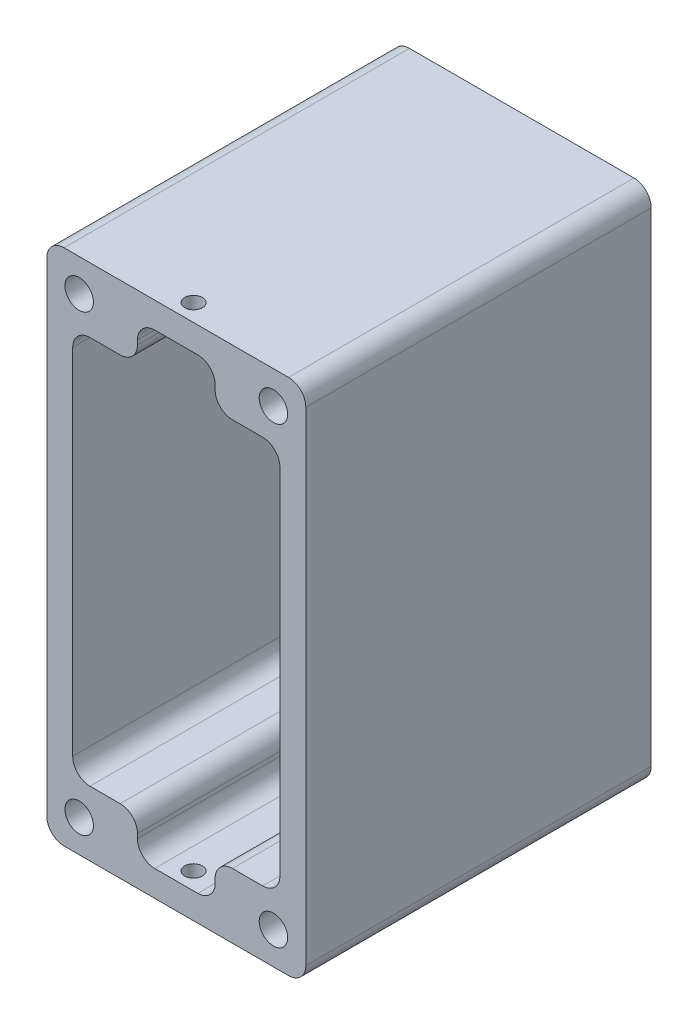
SolidWorks part; units mm, degrees
ref_plane "前视基准面" through (0, 0, 0) normal (0, 0, 1) x (1, 0, 0)
ref_plane "上视基准面" through (0, 0, 0) normal (0, 1, 0) x (1, 0, 0)
ref_plane "右视基准面" through (0, 0, 0) normal (1, 0, 0) x (0, 0, -1)
sketch "草图1" plane through (0, 0, 0) normal (0, 0, 1) x (1, 0, 0)
  line L0 (0, 30) -> (0, -19.5) construction
  line L1 (-12, 0) -> (12, 0) construction
  line L2 (12, 19.5) -> (12, 22.5)
  line L3 (7.5, 30) -> (-7.5, 30)
  line L4 (-12, -19.5) -> (-12, 19.5)
  line L5 (-15, 30) -> (-15, 22.5)
  line L6 (-7.5, 30) -> (-15, 30)
  line L7 (-7.5, 22.5) -> (-4.5, 22.5)
  line L8 (-4.5, 22.5) -> (-4.5, 27)
  line L9 (-15, 22.5) -> (-7.5, 22.5)
  line L10 (-7.5, 30) -> (-7.5, 22.5)
  line L11 (4.5, 27) -> (-4.5, 27)
  line L12 (15, 30) -> (7.5, 30)
  line L13 (15, 22.5) -> (7.5, 22.5)
  line L14 (7.5, 30) -> (7.5, 22.5)
  line L15 (15, 22.5) -> (15, 30)
  line L16 (12, -19.5) -> (12, 19.5)
  line L17 (-7.5, 30) -> (-7.5, 22.5)
  line L18 (-15, 22.5) -> (-7.5, 22.5)
  line L20 (7.5, 30) -> (7.5, 22.5)
  line L21 (15, 22.5) -> (7.5, 22.5)
  line L22 (4.5, 22.5) -> (4.5, 27)
  line L23 (7.5, 22.5) -> (4.5, 22.5)
  line L24 (0, -30) -> (0, 19.5) construction
  line L26 (-15, 22.5) -> (-15, 30)
  line L28 (-12, -19.5) -> (-12, -22.5)
  line L29 (-15, 30) -> (-7.5, 30)
  line L30 (7.5, 30) -> (15, 30)
  line L31 (15, 30) -> (15, 22.5)
  line L32 (-12, 19.5) -> (-12, 22.5)
  line L33 (15, -30) -> (15, -22.5)
  line L34 (7.5, -30) -> (15, -30)
  line L35 (-15, -30) -> (-7.5, -30)
  line L36 (-15, -22.5) -> (-15, -30)
  line L37 (7.5, -22.5) -> (4.5, -22.5)
  line L38 (4.5, -22.5) -> (4.5, -27)
  line L39 (15, -22.5) -> (7.5, -22.5)
  line L40 (7.5, -30) -> (7.5, -22.5)
  line L41 (-15, -22.5) -> (-7.5, -22.5)
  line L42 (-7.5, -30) -> (-7.5, -22.5)
  line L43 (15, -22.5) -> (15, -30)
  line L44 (7.5, -30) -> (7.5, -22.5)
  line L45 (15, -22.5) -> (7.5, -22.5)
  line L46 (15, -30) -> (7.5, -30)
  line L47 (4.5, -27) -> (-4.5, -27)
  line L48 (-7.5, -30) -> (-7.5, -22.5)
  line L49 (-15, -22.5) -> (-7.5, -22.5)
  line L50 (-4.5, -22.5) -> (-4.5, -27)
  line L51 (-7.5, -22.5) -> (-4.5, -22.5)
  line L52 (-7.5, -30) -> (-15, -30)
  line L53 (-15, -30) -> (-15, -22.5)
  line L54 (7.5, -30) -> (-7.5, -30)
  line L55 (12, -19.5) -> (12, -22.5)
  line L56 (-15, 22.5) -> (-15, -22.5)
  line L57 (15, 22.5) -> (15, -22.5)
  line L58 (-7.5, 22.5) -> (-4.5, 22.5)
  line L59 (-4.5, 22.5) -> (-4.5, 27)
  line L60 (4.5, 22.5) -> (4.5, 27)
  line L61 (7.5, 22.5) -> (4.5, 22.5)
  line L62 (-7.5, -22.5) -> (-4.5, -22.5)
  line L63 (-4.5, -22.5) -> (-4.5, -27)
  line L64 (4.5, -27) -> (-4.5, -27)
  line L65 (7.5, -22.5) -> (4.5, -22.5)
  line L66 (4.5, -22.5) -> (4.5, -27)
  circle A0 centre (0, 0) radius 6
  point P0 (0, 0)
extrude "凸台-拉伸1" add sketch "草图1" along normal blind 40 contours L23 L14 L3 L10 L7 L8 L11 L22 | L10 L6 L5 L9 L18 | L13 L15 L12 L14 | L57 L13 L2 L16 L55 L39 | L9 L56 L41 L28 L4 L32 | L35 L42 L41 L36 | L40 L34 L33 L39 L45 | L54 L40 L37 L38 L47 L50 L51 L42
sketch "草图2" plane through (0, 0, 0) normal (0, 0, -1) x (-1, 0, 0)
  line L4 (-15, -30) -> (15, -30)
  line L5 (15, -30) -> (15, 30)
  line L6 (15, 30) -> (-15, 30)
  line L7 (-15, 30) -> (-15, -30)
  line L8 (-15, -30) -> (15, -30)
  line L9 (15, -30) -> (15, 30)
  line L10 (15, 30) -> (-15, 30)
  line L11 (-15, 30) -> (-15, -30)
  line L36 (-12, -22.5) -> (-4.5, -22.5)
  line L37 (-12, 22.5) -> (-12, -22.5)
  line L38 (-4.5, 22.5) -> (-12, 22.5)
  line L39 (-4.5, 27) -> (-4.5, 22.5)
  line L40 (4.5, 27) -> (-4.5, 27)
  line L41 (4.5, 22.5) -> (4.5, 27)
  line L42 (12, 22.5) -> (4.5, 22.5)
  line L43 (12, -22.5) -> (12, 22.5)
  line L44 (4.5, -22.5) -> (12, -22.5)
  line L45 (4.5, -27) -> (4.5, -22.5)
  line L46 (-4.5, -27) -> (4.5, -27)
  line L47 (-4.5, -22.5) -> (-4.5, -27)
  line L48 (-12, -22.5) -> (-4.5, -22.5)
  line L49 (-12, 22.5) -> (-12, -22.5)
  line L50 (-4.5, 22.5) -> (-12, 22.5)
  line L51 (-4.5, 27) -> (-4.5, 22.5)
  line L52 (4.5, 27) -> (-4.5, 27)
  line L53 (4.5, 22.5) -> (4.5, 27)
  line L54 (12, 22.5) -> (4.5, 22.5)
  line L55 (12, -22.5) -> (12, 22.5)
  line L56 (4.5, -22.5) -> (12, -22.5)
  line L57 (4.5, -27) -> (4.5, -22.5)
  line L58 (-4.5, -27) -> (4.5, -27)
  line L59 (-4.5, -22.5) -> (-4.5, -27)
  dimension "D1" = 0
  dimension "D2" = 0
fillet "圆角1" radius 2 12 edges at (12, 22.5, 20) (12, -22.5, 20) (4.5, -22.5, 20) (4.5, -27, 20) (-4.5, -27, 20) (-4.5, -22.5, 20) (-12, -22.5, 20) (-12, 22.5, 20) (-4.5, 22.5, 20) (-4.5, 27, 20) (4.5, 27, 20) (4.5, 22.5, 20)
ref_plane "基准面1" through (0, 30, 0) normal (0, 1, 0) x (1, 0, 0)
sketch "草图3" plane through (0, 30, 0) normal (0, 1, 0) x (1, 0, 0)
  line L0 (0, -28) -> (1.1542, -28) construction
  line L4 (0, -30) -> (0, -26) construction
hole_wizard "M2.5 螺纹孔1" positions "草图10" profile "草图11" tap size "M2.5" standard "GB" end condition through all
sketch "草图10" plane through (0, 30, 0) normal (0, 1, 0) x (1, 0, 0)
  point P0 (0, -38)
sketch "草图11" plane through (0, 30, 38) normal (1, 0, 0) x (0, 0, 1)
  line L0 (0, 0) -> (0, 60)
  line L1 (0, 60) -> (1.025, 60)
  line L2 (1.025, 60) -> (1.025, 0)
  line L5 (1.025, 0) -> (0, 0)
  line L11 (0, -6.35) -> (0, 107.95) construction
  dimension "通孔螺纹孔钻头直径" = 2.05
  dimension "通孔螺纹孔钻头深度" = 60
cosmetic thread "孔螺蚊线1" parameters "D2"=2.5
sketch "草图12" plane through (0, 0, 0) normal (0, 0, 1) x (1, 0, 0)
  circle A17 centre (-11.25, -26.25) radius 1.65
  circle A19 centre (11.25, -26.25) radius 1.65
  circle A21 centre (11.25, 26.25) radius 1.65
  circle A23 centre (-11.25, 26.25) radius 1.65
hole_wizard "M4 螺纹孔1" positions "草图13" profile "草图14" tap size "M4" standard "GB"
sketch "草图13" plane through (0, 0, 0) normal (0, 0, -1) x (-1, 0, 0)
  point P0 (-11.25, 26.25)
  point P3 (11.25, 26.25)
  point P6 (11.25, -26.25)
  point P9 (-11.25, -26.25)
sketch "草图14" plane through (11.25, 26.25, 0) normal (1, 0, 0) x (0, 1, 0)
  line L0 (0, 0) -> (0, 8.9914)
  line L1 (0, 8.9914) -> (1.65, 8)
  line L2 (1.65, 8) -> (1.65, 0)
  line L5 (1.65, 0) -> (0, 0)
  line L10 (0, 8.9914) -> (-1.65, 8) construction
  line L11 (0, -6.35) -> (0, 107.95) construction
  dimension "螺纹孔钻头直径" = 3.3
  dimension "螺纹孔钻头深度" = 8
  dimension "导头角度" = 118
cosmetic thread "孔螺蚊线2" parameters "D1"=8, "D2"=4
cosmetic thread "孔螺蚊线3" parameters "D1"=8, "D2"=4
cosmetic thread "孔螺蚊线4" parameters "D1"=8, "D2"=4
cosmetic thread "孔螺蚊线5" parameters "D1"=8, "D2"=4
ref_plane "基准面2" through (0, 0, 20) normal (0, 0, -1) x (-1, 0, 0)
mirror "镜向1" about plane through (0, 0, 20) normal (0, 0, -1) of "M4 螺纹孔1"
fillet "圆角2" radius 2 4 edges at (15, -30, 20) (-15, -30, 20) (-15, 30, 20) (15, 30, 20)
